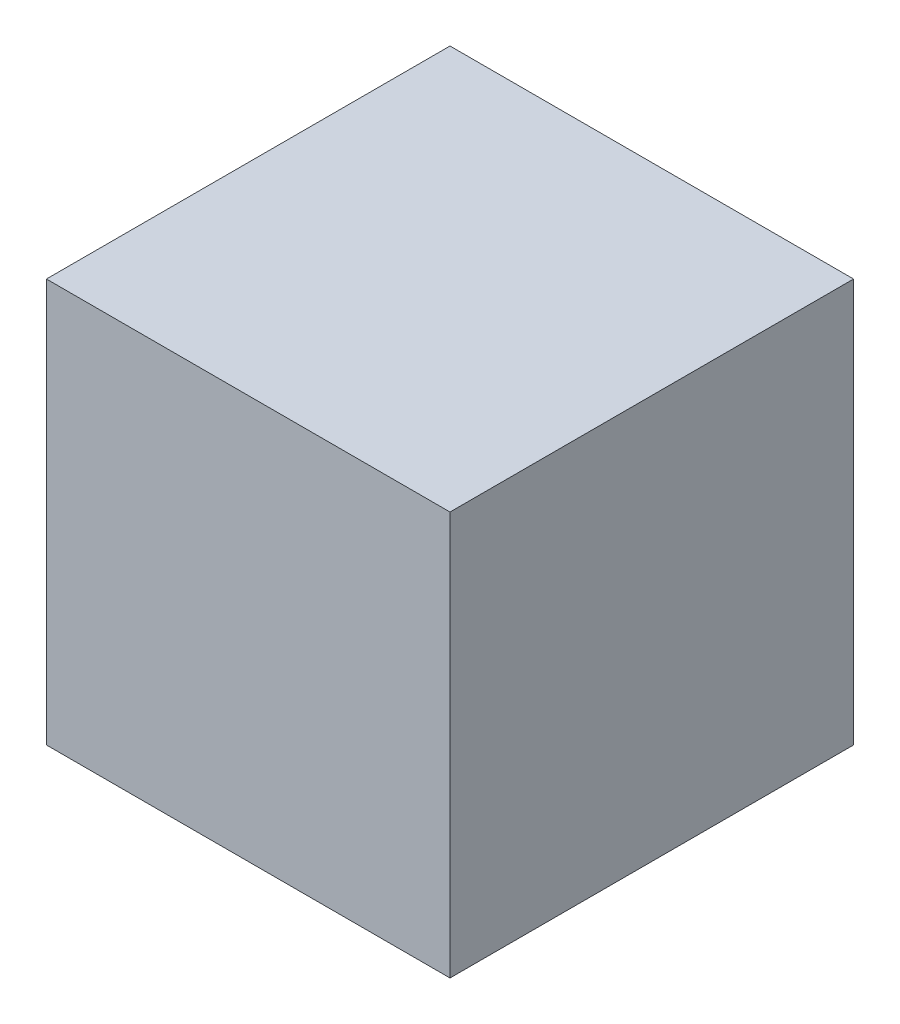
SolidWorks part; units mm, degrees
ref_plane "Front Plane" through (0, 0, 0) normal (0, 0, 1) x (1, 0, 0)
ref_plane "Top Plane" through (0, 0, 0) normal (0, 1, 0) x (1, 0, 0)
ref_plane "Right Plane" through (0, 0, 0) normal (1, 0, 0) x (0, 0, -1)
sketch "Sketch1" plane through (0, 0, 0) normal (0, 1, 0) x (1, 0, 0)
  line L0 (0, -15) -> (0, 15) construction
  line L1 (-15, 0) -> (15, 0) construction
  line L2 (60, -15) -> (60, 15) construction
  line L3 (-60, -15) -> (-60, 15) construction
  line L4 (-15, -60) -> (15, -60) construction
  line L5 (-15, 60) -> (15, 60) construction
  point P4 (0, 0)
  point P8 (0, 0)
  dimension "D1" = 60
  dimension "D2" = 60
  dimension "D3" = 60
  dimension "D4" = 60
sketch "Sketch2" plane through (0, 0, 0) normal (0, 0, 1) x (1, 0, 0)
  line L0 (0, -15) -> (0, 15) construction
  line L2 (60, -15) -> (60, 15) construction
  line L3 (-60, -15) -> (-60, 15) construction
  point P3 (0, 0)
  dimension "D1" = 60
  dimension "D2" = 60
ref_plane "Plane1" through (0, 60, 0) normal (0, 1, 0) x (1, 0, 0)
sketch "Sketch3" plane through (0, 60, 0) normal (0, 1, 0) x (1, 0, 0)
  line L0 (0, -15) -> (0, 15) construction
  line L5 (0, 0) -> (-10, 0)
  line L6 (0, 0) -> (0, -10)
  line L7 (0, -10) -> (-10, -10)
  line L8 (-10, 0) -> (-10, -10)
  dimension "D1" = 10
  dimension "D2" = 10
extrude "alignment Cube" add sketch "Sketch3" against normal blind 10
